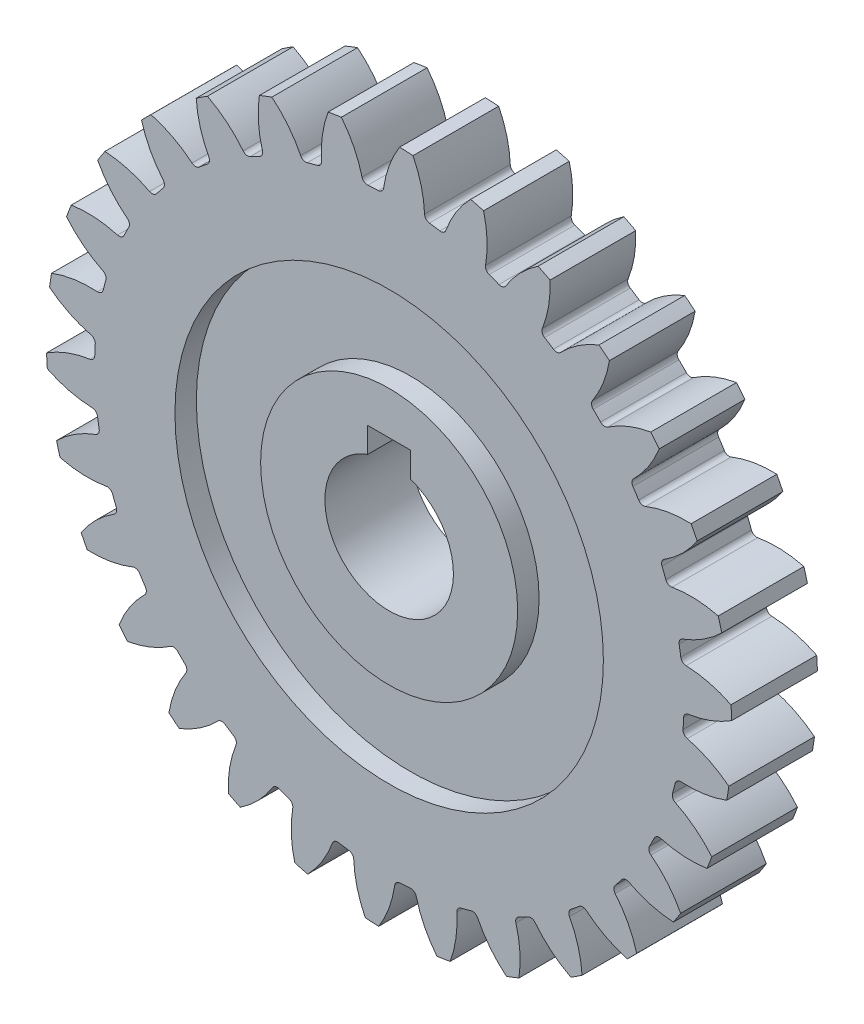
SolidWorks part; units mm, degrees
ref_plane "Front Plane" through (0, 0, 0) normal (0, 0, 1) x (1, 0, 0)
ref_plane "Top Plane" through (0, 0, 0) normal (0, 1, 0) x (1, 0, 0)
ref_plane "Right Plane" through (0, 0, 0) normal (1, 0, 0) x (0, 0, -1)
sketch "Sketch1" plane through (0, 0, 0) normal (0, 0, 1) x (1, 0, 0)
  circle A0 centre (0, 0) radius 80
extrude "Boss-Extrude2" add sketch "Sketch1" along normal mid plane 20
sketch "Sketch2" plane through (0, 0, 10) normal (0, 0, 1) x (1, 0, 0)
  arc A1 (-2.5333, 68.7033) -> (-4.9794, 68.5694) centre (0, 0) ccw
  arc A2 (2.4407, 79.9628) -> (-1.294, 69.8203) centre (24.1045, 66.2267) ccw
  arc A3 (2.4407, 79.9628) -> (-11.1524, 79.2188) centre (0, 0) ccw
  arc A4 (-11.1524, 79.2188) -> (-6.3332, 69.5445) centre (-31.1878, 63.2006) cw
  arc A5 (-1.424, 68.7353) -> (-6.0855, 68.4801) centre (0, 0) ccw
  arc A6 (-1.294, 69.8203) -> (-2.5333, 68.7033) centre (-2.5812, 70.0024) cw
  arc A7 (-6.3332, 69.5445) -> (-4.9794, 68.5694) centre (-5.0735, 69.866) ccw
  arc A8 (5.5618, 79.8064) -> (8.2644, 69.3415) centre (-17.3662, 68.3039) cw
  arc A9 (8.2644, 69.3415) -> (9.3858, 68.1063) centre (9.5633, 69.3941) ccw
  arc A10 (19.0126, 77.7079) -> (5.5618, 79.8064) centre (0, 0) ccw
  arc A11 (19.0126, 77.7079) -> (13.2507, 68.5636) centre (37.3471, 59.7678) ccw
  arc A12 (13.2507, 68.5636) -> (11.8063, 67.7287) centre (12.0295, 69.0094) cw
  arc A13 (11.8063, 67.7287) -> (9.3858, 68.1063) centre (0, 0) ccw
  arc A14 (22.0329, 76.9061) -> (22.5007, 66.108) centre (-2.7855, 70.4219) cw
  arc A15 (22.5007, 66.108) -> (23.3408, 64.6666) centre (23.7822, 65.8894) ccw
  arc A16 (34.7535, 72.0569) -> (22.0329, 76.9061) centre (0, 0) ccw
  arc A17 (34.7535, 72.0569) -> (27.2163, 64.3103) centre (48.9574, 50.6969) ccw
  arc A18 (27.2163, 64.3103) -> (25.6299, 63.794) centre (26.1145, 65.0003) cw
  arc A19 (25.6299, 63.794) -> (23.3408, 64.6666) centre (0, 0) ccw
  arc A20 (37.5411, 70.6446) -> (35.7536, 59.9852) centre (11.9169, 69.4621) cw
  arc A21 (35.7536, 59.9852) -> (36.2757, 58.4007) centre (36.9616, 59.505) ccw
  arc A22 (48.9755, 63.2566) -> (37.5411, 70.6446) centre (0, 0) ccw
  arc A23 (48.9755, 63.2566) -> (39.9925, 57.2464) centre (58.428, 39.4102) ccw
  arc A24 (39.9925, 57.2464) -> (38.3333, 57.0712) centre (39.0582, 58.1503) cw
  arc A25 (38.3333, 57.0712) -> (36.2757, 58.4007) centre (0, 0) ccw
  arc A26 (51.4086, 61.2956) -> (47.4439, 51.2408) centre (26.0985, 65.4666) cw
  arc A27 (47.4439, 51.2408) -> (47.6252, 49.5823) centre (48.5257, 50.5199) ccw
  arc A28 (61.0571, 51.6917) -> (51.4086, 61.2956) centre (0, 0) ccw
  arc A29 (61.0571, 51.6917) -> (51.0207, 47.6805) centre (65.3451, 26.4011) ccw
  arc A30 (51.0207, 47.6805) -> (49.3614, 47.8541) centre (50.2948, 48.759) cw
  arc A31 (49.3614, 47.8541) -> (47.6252, 49.5823) centre (0, 0) ccw
  arc A32 (63.0293, 49.2677) -> (57.0607, 40.2569) centre (39.1394, 58.6098) cw
  arc A33 (57.0607, 40.2569) -> (56.8932, 38.597) centre (57.969, 39.3268) ccw
  arc A34 (70.4702, 37.8676) -> (63.0293, 49.2677) centre (0, 0) ccw
  arc A35 (70.4702, 37.8676) -> (59.8192, 36.0308) centre (69.4062, 12.2382) ccw
  arc A36 (59.8192, 36.0308) -> (58.2322, 36.5455) centre (59.3333, 37.2366) cw
  arc A37 (58.2322, 36.5455) -> (56.8932, 38.597) centre (0, 0) ccw
  arc A38 (71.8953, 35.0866) -> (64.1837, 27.5136) centre (50.4698, 49.1915) cw
  arc A39 (64.1837, 27.5136) -> (63.6747, 25.9248) centre (64.8787, 26.415) ccw
  arc A40 (76.8033, 22.3886) -> (71.8953, 35.0866) centre (0, 0) ccw
  arc A41 (76.8033, 22.3886) -> (66.0032, 22.8063) centre (70.434, -2.4596) ccw
  arc A42 (66.0032, 22.8063) -> (64.5579, 23.6398) centre (65.7786, 24.0868) cw
  arc A43 (64.5579, 23.6398) -> (63.6747, 25.9248) centre (0, 0) ccw
  arc A44 (77.6191, 19.372) -> (68.5016, 13.5678) centre (59.5944, 37.6232) cw
  arc A45 (68.5016, 13.5678) -> (67.6733, 12.1196) centre (68.953, 12.3487) ccw
  arc A46 (79.7798, 5.931) -> (77.6191, 19.372) centre (0, 0) ccw
  arc A47 (79.7798, 5.931) -> (69.3026, 8.5851) centre (68.3835, -17.0499) ccw
  arc A48 (69.3026, 8.5851) -> (68.0621, 9.7009) centre (69.3491, 9.8843) cw
  arc A49 (68.0621, 9.7009) -> (67.6733, 12.1196) centre (0, 0) ccw
  arc A50 (79.9506, 2.8107) -> (69.8255, -0.9709) centre (66.1144, 24.4107) cw
  arc A51 (69.8255, -0.9709) -> (68.7143, -2.2154) centre (70.0136, -2.2572) ccw
  arc A52 (79.2696, -10.7858) -> (79.9506, 2.8107) centre (0, 0) ccw
  arc A53 (79.2696, -10.7858) -> (69.5731, -6.0113) centre (63.3443, -30.8951) ccw
  arc A54 (69.5731, -6.0113) -> (68.5917, -4.662) centre (69.8888, -4.7502) cw
  arc A55 (68.5917, -4.662) -> (68.7143, -2.2154) centre (0, 0) ccw
  arc A56 (78.7879, -13.8734) -> (68.0978, -15.4672) centre (69.7449, 10.1313) cw
  arc A57 (68.0978, -15.4672) -> (66.7521, -16.4534) centre (68.0144, -16.7646) ccw
  arc A58 (75.2949, -27.0311) -> (78.7879, -13.8734) centre (0, 0) ccw
  arc A59 (75.2949, -27.0311) -> (66.8029, -20.345) centre (55.5366, -43.3899) ccw
  arc A60 (66.8029, -20.345) -> (66.1236, -18.8212) centre (67.3739, -19.1771) cw
  arc A61 (66.1236, -18.8212) -> (66.7521, -16.4534) centre (0, 0) ccw
  arc A62 (74.1817, -29.9511) -> (63.3939, -29.2876) centre (70.3273, -4.5909) cw
  arc A63 (63.3939, -29.2876) -> (61.8726, -29.9724) centre (63.0425, -30.5392) ccw
  arc A64 (68.0294, -42.0951) -> (74.1817, -29.9511) centre (0, 0) ccw
  arc A65 (68.0294, -42.0951) -> (61.1132, -33.7895) centre (45.3017, -53.9885) ccw
  arc A66 (61.1132, -33.7895) -> (60.7655, -32.1578) centre (61.9145, -32.7658) cw
  arc A67 (60.7655, -32.1578) -> (61.8726, -29.9724) centre (0, 0) ccw
  arc A68 (66.3335, -44.7199) -> (55.9194, -41.8279) centre (67.836, -19.1124) cw
  arc A69 (55.9194, -41.8279) -> (54.2889, -42.1815) centre (55.3154, -42.9791) ccw
  arc A70 (57.7907, -55.3194) -> (66.3335, -44.7199) centre (0, 0) ccw
  arc A71 (57.7907, -55.3194) -> (52.7525, -45.7573) centre (33.0869, -62.2275) ccw
  arc A72 (52.7525, -45.7573) -> (52.7516, -44.0889) centre (53.7491, -44.9226) cw
  arc A73 (52.7516, -44.0889) -> (54.2889, -42.1815) centre (0, 0) ccw
  arc A74 (55.5862, -57.5341) -> (46.0009, -52.5402) centre (62.3799, -32.7986) cw
  arc A75 (46.0009, -52.5402) -> (44.3325, -52.547) centre (45.1708, -53.5407) ccw
  arc A76 (45.0263, -66.1259) -> (55.5862, -57.5341) centre (0, 0) ccw
  arc A77 (45.0263, -66.1259) -> (42.0862, -55.7252) centre (19.4261, -67.7468) ccw
  arc A78 (42.0862, -55.7252) -> (42.4323, -54.0931) centre (43.2346, -55.116) cw
  arc A79 (42.4323, -54.0931) -> (44.3325, -52.547) centre (0, 0) ccw
  arc A80 (42.4095, -67.8339) -> (34.0719, -60.9562) centre (54.1975, -45.0514) cw
  arc A81 (34.0719, -60.9562) -> (32.4386, -60.616) centre (33.052, -61.7622) ccw
  arc A82 (30.2941, -74.0424) -> (42.4095, -67.8339) centre (0, 0) ccw
  arc A83 (30.2941, -74.0424) -> (29.5806, -63.2577) centre (4.9162, -70.3053) ccw
  arc A84 (29.5806, -63.2577) -> (30.2584, -61.7332) centre (30.8306, -62.9005) cw
  arc A85 (30.2584, -61.7332) -> (32.4386, -60.616) centre (0, 0) ccw
  arc A86 (27.3793, -75.169) -> (20.6539, -66.7081) centre (43.6465, -55.3352) cw
  arc A87 (20.6539, -66.7081) -> (19.127, -66.0358) centre (19.4886, -67.2844) ccw
  arc A88 (14.2378, -78.7228) -> (27.3793, -75.169) centre (0, 0) ccw
  arc A89 (14.2378, -78.7228) -> (15.7822, -68.0255) centre (-9.8085, -69.7911) ccw
  arc A90 (15.7822, -68.0255) -> (16.7621, -66.6753) centre (17.0791, -67.936) cw
  arc A91 (16.7621, -66.6753) -> (19.127, -66.0358) centre (0, 0) ccw
  arc A92 (11.1524, -79.2188) -> (6.3332, -69.5445) centre (31.1878, -63.2006) cw
  arc A93 (6.3332, -69.5445) -> (4.9794, -68.5694) centre (5.0735, -69.866) ccw
  arc A94 (-2.4407, -79.9628) -> (11.1524, -79.2188) centre (0, 0) ccw
  arc A95 (-2.4407, -79.9628) -> (1.294, -69.8203) centre (-24.1045, -66.2267) ccw
  arc A96 (1.294, -69.8203) -> (2.5333, -68.7033) centre (2.5812, -70.0024) cw
  arc A97 (2.5333, -68.7033) -> (4.9794, -68.5694) centre (0, 0) ccw
  arc A98 (-5.5618, -79.8064) -> (-8.2644, -69.3415) centre (17.3662, -68.3039) cw
  arc A99 (-8.2644, -69.3415) -> (-9.3858, -68.1063) centre (-9.5633, -69.3941) ccw
  arc A100 (-19.0126, -77.7079) -> (-5.5618, -79.8064) centre (0, 0) ccw
  arc A101 (-19.0126, -77.7079) -> (-13.2507, -68.5636) centre (-37.3471, -59.7678) ccw
  arc A102 (-13.2507, -68.5636) -> (-11.8063, -67.7287) centre (-12.0295, -69.0094) cw
  arc A103 (-11.8063, -67.7287) -> (-9.3858, -68.1063) centre (0, 0) ccw
  arc A104 (-22.0329, -76.9061) -> (-22.5007, -66.108) centre (2.7855, -70.4219) cw
  arc A105 (-22.5007, -66.108) -> (-23.3408, -64.6666) centre (-23.7822, -65.8894) ccw
  arc A106 (-34.7535, -72.0569) -> (-22.0329, -76.9061) centre (0, 0) ccw
  arc A107 (-34.7535, -72.0569) -> (-27.2163, -64.3103) centre (-48.9574, -50.6969) ccw
  arc A108 (-27.2163, -64.3103) -> (-25.6299, -63.794) centre (-26.1145, -65.0003) cw
  arc A109 (-25.6299, -63.794) -> (-23.3408, -64.6666) centre (0, 0) ccw
  arc A110 (-37.5411, -70.6446) -> (-35.7536, -59.9852) centre (-11.9169, -69.4621) cw
  arc A111 (-35.7536, -59.9852) -> (-36.2757, -58.4007) centre (-36.9616, -59.505) ccw
  arc A112 (-48.9755, -63.2566) -> (-37.5411, -70.6446) centre (0, 0) ccw
  arc A113 (-48.9755, -63.2566) -> (-39.9925, -57.2464) centre (-58.428, -39.4102) ccw
  arc A114 (-39.9925, -57.2464) -> (-38.3333, -57.0712) centre (-39.0582, -58.1503) cw
  arc A115 (-38.3333, -57.0712) -> (-36.2757, -58.4007) centre (0, 0) ccw
  arc A116 (-51.4086, -61.2956) -> (-47.4439, -51.2408) centre (-26.0985, -65.4666) cw
  arc A117 (-47.4439, -51.2408) -> (-47.6252, -49.5823) centre (-48.5257, -50.5199) ccw
  arc A118 (-61.0571, -51.6917) -> (-51.4086, -61.2956) centre (0, 0) ccw
  arc A119 (-61.0571, -51.6917) -> (-51.0207, -47.6805) centre (-65.3451, -26.4011) ccw
  arc A120 (-51.0207, -47.6805) -> (-49.3614, -47.8541) centre (-50.2948, -48.759) cw
  arc A121 (-49.3614, -47.8541) -> (-47.6252, -49.5823) centre (0, 0) ccw
  arc A122 (-63.0293, -49.2677) -> (-57.0607, -40.2569) centre (-39.1394, -58.6098) cw
  arc A123 (-57.0607, -40.2569) -> (-56.8932, -38.597) centre (-57.969, -39.3268) ccw
  arc A124 (-70.4702, -37.8676) -> (-63.0293, -49.2677) centre (0, 0) ccw
  arc A125 (-70.4702, -37.8676) -> (-59.8192, -36.0308) centre (-69.4062, -12.2382) ccw
  arc A126 (-59.8192, -36.0308) -> (-58.2322, -36.5455) centre (-59.3333, -37.2366) cw
  arc A127 (-58.2322, -36.5455) -> (-56.8932, -38.597) centre (0, 0) ccw
  arc A128 (-71.8953, -35.0866) -> (-64.1837, -27.5136) centre (-50.4698, -49.1915) cw
  arc A129 (-64.1837, -27.5136) -> (-63.6747, -25.9248) centre (-64.8787, -26.415) ccw
  arc A130 (-76.8033, -22.3886) -> (-71.8953, -35.0866) centre (0, 0) ccw
  arc A131 (-76.8033, -22.3886) -> (-66.0032, -22.8063) centre (-70.434, 2.4596) ccw
  arc A132 (-66.0032, -22.8063) -> (-64.5579, -23.6398) centre (-65.7786, -24.0868) cw
  arc A133 (-64.5579, -23.6398) -> (-63.6747, -25.9248) centre (0, 0) ccw
  arc A134 (-77.6191, -19.372) -> (-68.5016, -13.5678) centre (-59.5944, -37.6232) cw
  arc A135 (-68.5016, -13.5678) -> (-67.6733, -12.1196) centre (-68.953, -12.3487) ccw
  arc A136 (-79.7798, -5.931) -> (-77.6191, -19.372) centre (0, 0) ccw
  arc A137 (-79.7798, -5.931) -> (-69.3026, -8.5851) centre (-68.3835, 17.0499) ccw
  arc A138 (-69.3026, -8.5851) -> (-68.0621, -9.7009) centre (-69.3491, -9.8843) cw
  arc A139 (-68.0621, -9.7009) -> (-67.6733, -12.1196) centre (0, 0) ccw
  arc A140 (-79.9506, -2.8107) -> (-69.8255, 0.9709) centre (-66.1144, -24.4107) cw
  arc A141 (-69.8255, 0.9709) -> (-68.7143, 2.2154) centre (-70.0136, 2.2572) ccw
  arc A142 (-79.2696, 10.7858) -> (-79.9506, -2.8107) centre (0, 0) ccw
  arc A143 (-79.2696, 10.7858) -> (-69.5731, 6.0113) centre (-63.3443, 30.8951) ccw
  arc A144 (-69.5731, 6.0113) -> (-68.5917, 4.662) centre (-69.8888, 4.7502) cw
  arc A145 (-68.5917, 4.662) -> (-68.7143, 2.2154) centre (0, 0) ccw
  arc A146 (-78.7879, 13.8734) -> (-68.0978, 15.4672) centre (-69.7449, -10.1313) cw
  arc A147 (-68.0978, 15.4672) -> (-66.7521, 16.4534) centre (-68.0144, 16.7646) ccw
  arc A148 (-75.2949, 27.0311) -> (-78.7879, 13.8734) centre (0, 0) ccw
  arc A149 (-75.2949, 27.0311) -> (-66.8029, 20.345) centre (-55.5366, 43.3899) ccw
  arc A150 (-66.8029, 20.345) -> (-66.1236, 18.8212) centre (-67.3739, 19.1771) cw
  arc A151 (-66.1236, 18.8212) -> (-66.7521, 16.4534) centre (0, 0) ccw
  arc A152 (-74.1817, 29.9511) -> (-63.3939, 29.2876) centre (-70.3273, 4.5909) cw
  arc A153 (-63.3939, 29.2876) -> (-61.8726, 29.9724) centre (-63.0425, 30.5392) ccw
  arc A154 (-68.0294, 42.0951) -> (-74.1817, 29.9511) centre (0, 0) ccw
  arc A155 (-68.0294, 42.0951) -> (-61.1132, 33.7895) centre (-45.3017, 53.9885) ccw
  arc A156 (-61.1132, 33.7895) -> (-60.7655, 32.1578) centre (-61.9145, 32.7658) cw
  arc A157 (-60.7655, 32.1578) -> (-61.8726, 29.9724) centre (0, 0) ccw
  arc A158 (-66.3335, 44.7199) -> (-55.9194, 41.8279) centre (-67.836, 19.1124) cw
  arc A159 (-55.9194, 41.8279) -> (-54.2889, 42.1815) centre (-55.3154, 42.9791) ccw
  arc A160 (-57.7907, 55.3194) -> (-66.3335, 44.7199) centre (0, 0) ccw
  arc A161 (-57.7907, 55.3194) -> (-52.7525, 45.7573) centre (-33.0869, 62.2275) ccw
  arc A162 (-52.7525, 45.7573) -> (-52.7516, 44.0889) centre (-53.7491, 44.9226) cw
  arc A163 (-52.7516, 44.0889) -> (-54.2889, 42.1815) centre (0, 0) ccw
  arc A164 (-55.5862, 57.5341) -> (-46.0009, 52.5402) centre (-62.3799, 32.7986) cw
  arc A165 (-46.0009, 52.5402) -> (-44.3325, 52.547) centre (-45.1708, 53.5407) ccw
  arc A166 (-45.0263, 66.1259) -> (-55.5862, 57.5341) centre (0, 0) ccw
  arc A167 (-45.0263, 66.1259) -> (-42.0862, 55.7252) centre (-19.4261, 67.7468) ccw
  arc A168 (-42.0862, 55.7252) -> (-42.4323, 54.0931) centre (-43.2346, 55.116) cw
  arc A169 (-42.4323, 54.0931) -> (-44.3325, 52.547) centre (0, 0) ccw
  arc A170 (-42.4095, 67.8339) -> (-34.0719, 60.9562) centre (-54.1975, 45.0514) cw
  arc A171 (-34.0719, 60.9562) -> (-32.4386, 60.616) centre (-33.052, 61.7622) ccw
  arc A172 (-30.2941, 74.0424) -> (-42.4095, 67.8339) centre (0, 0) ccw
  arc A173 (-30.2941, 74.0424) -> (-29.5806, 63.2577) centre (-4.9162, 70.3053) ccw
  arc A174 (-29.5806, 63.2577) -> (-30.2584, 61.7332) centre (-30.8306, 62.9005) cw
  arc A175 (-30.2584, 61.7332) -> (-32.4386, 60.616) centre (0, 0) ccw
  arc A176 (-27.3793, 75.169) -> (-20.6539, 66.7081) centre (-43.6465, 55.3352) cw
  arc A177 (-20.6539, 66.7081) -> (-19.127, 66.0358) centre (-19.4886, 67.2844) ccw
  arc A178 (-14.2378, 78.7228) -> (-27.3793, 75.169) centre (0, 0) ccw
  arc A179 (-14.2378, 78.7228) -> (-15.7822, 68.0255) centre (9.8085, 69.7911) ccw
  arc A180 (-15.7822, 68.0255) -> (-16.7621, 66.6753) centre (-17.0791, 67.936) cw
  arc A181 (-16.7621, 66.6753) -> (-19.127, 66.0358) centre (0, 0) ccw
  point P307 (0, 0)
  circle M1 centre (0, 0) radius 80
  dimension "D1" = 137.5
  dimension "D2" = 1.3
  dimension "D3" = 30
extrude "Cut-Extrude1" cut sketch "Sketch2" against normal up to next (20 mm away) contours A13 A12 A11 A8 A9 M1 | A4 A7 A1 A6 A2 M1 | A181 A180 A179 A176 A177 M1 | A175 A174 A173 A170 A171 M1 | A169 A168 A167 A164 A165 M1 | A163 A162 A161 A158 A159 M1 | A157 A156 A155 A152 A153 M1 | A151 A150 A149 A146 A147 M1 | A145 A144 A143 A140 A141 M1 | A139 A138 A137 A134 A135 M1 | A133 A132 A131 A128 A129 M1 | A127 A126 A125 A122 A123 M1 | A121 A120 A119 A116 A117 M1 | A115 A114 A113 A110 A111 M1 | A109 A108 A107 A104 A105 M1 | A103 A102 A101 A98 A99 M1 | A97 A96 A95 A92 A93 M1 | A91 A90 A89 A86 A87 M1 | A85 A84 A83 A80 A81 M1 | A79 A78 A77 A74 A75 M1 | A73 A72 A71 A68 A69 M1 | A67 A66 A65 A62 A63 M1 | A61 A60 A59 A56 A57 M1 | A55 A54 A53 A50 A51 M1 | A49 A48 A47 A44 A45 M1 | A43 A42 A41 A38 A39 M1 | A37 A36 A35 A32 A33 M1 | A31 A30 A29 A26 A27 M1 | A25 A24 A23 A20 A21 M1 | A19 A18 A17 A14 A15 M1
sketch "Sketch3" plane through (0, 0, 10) normal (0, 0, 1) x (1, 0, 0)
  circle A0 centre (0, 0) radius 50
extrude "Cut-Extrude2" cut sketch "Sketch3" against normal blind 5
sketch "Sketch4" plane through (0, 0, 5) normal (0, 0, 1) x (1, 0, 0)
  circle A0 centre (0, 0) radius 15
extrude "Cut-Extrude3" cut sketch "Sketch4" against normal through all
sketch "Sketch5" plane through (0, 0, 5) normal (0, 0, 1) x (1, 0, 0)
  circle A0 centre (0, 0) radius 15
  circle A1 centre (0, 0) radius 30
extrude "Boss-Extrude3" add sketch "Sketch5" along normal blind 5
sketch "Sketch6" plane through (0, 0, 10) normal (0, 0, 1) x (1, 0, 0)
  line L1 (5, 10) -> (-5, 10)
  line L2 (5, 10) -> (5, 20)
  line L3 (5, 20) -> (-5, 20)
  line L4 (-5, 10) -> (-5, 20)
  line L5 (5, 10) -> (-5, 20) construction
  line L6 (5, 20) -> (-5, 10) construction
  circle A0 centre (0, 0) radius 15 construction
  point P0 (0, 15)
  dimension "D1" = 10
  dimension "D2" = 10
extrude "Cut-Extrude4" cut sketch "Sketch6" against normal through all
